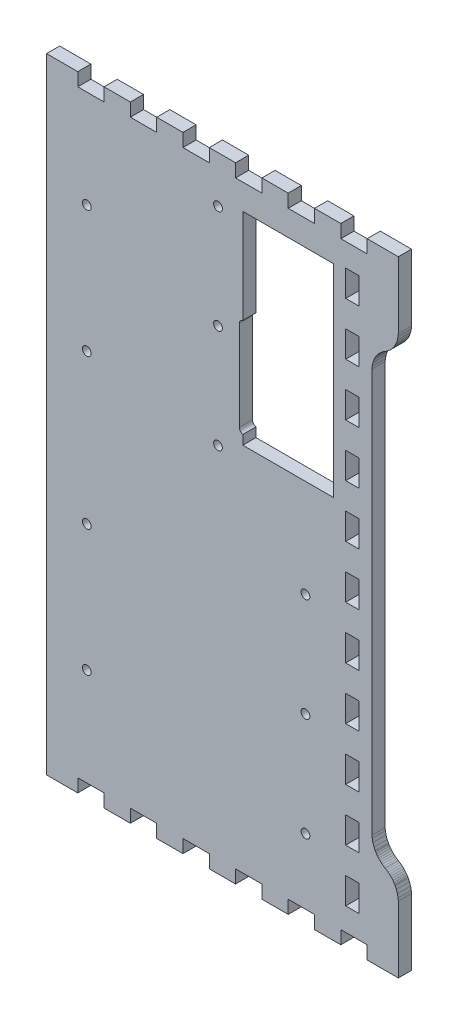
SolidWorks part; units mm, degrees
ref_plane "Front Plane" through (0, 0, 0) normal (0, 0, 1) x (1, 0, 0)
ref_plane "Top Plane" through (0, 0, 0) normal (0, 1, 0) x (1, 0, 0)
ref_plane "Right Plane" through (0, 0, 0) normal (1, 0, 0) x (0, 0, -1)
sketch "Model" plane through (0, 0, 0) normal (0, 0, 1) x (1, 0, 0)
  line L947 (1382.75, 22.8575) -> (1396.32, 22.8575)
  line L948 (1396.32, 22.8575) -> (1396.32, 28.5722)
  line L949 (1396.32, 28.5722) -> (1407.75, 28.5722)
  line L950 (1407.75, 28.5722) -> (1407.75, 22.8575)
  line L951 (1407.75, 22.8575) -> (1419.18, 22.8575)
  line L952 (1419.18, 22.8575) -> (1419.18, 28.5722)
  line L953 (1419.18, 28.5722) -> (1430.61, 28.5722)
  line L954 (1430.61, 28.5722) -> (1430.61, 22.8575)
  line L955 (1430.61, 22.8575) -> (1442.04, 22.8575)
  line L956 (1442.04, 22.8575) -> (1442.04, 28.5722)
  line L957 (1442.04, 28.5722) -> (1453.47, 28.5722)
  line L958 (1453.47, 28.5722) -> (1453.47, 22.8575)
  line L959 (1453.47, 22.8575) -> (1464.9, 22.8575)
  line L960 (1464.9, 22.8575) -> (1464.9, 28.5722)
  line L961 (1464.9, 28.5722) -> (1476.33, 28.5722)
  line L962 (1476.33, 28.5722) -> (1476.33, 22.8575)
  line L963 (1476.33, 22.8575) -> (1487.76, 22.8575)
  line L964 (1487.76, 22.8575) -> (1487.76, 28.5722)
  line L965 (1487.76, 28.5722) -> (1499.19, 28.5722)
  line L966 (1499.19, 28.5722) -> (1499.19, 22.8575)
  line L967 (1499.19, 22.8575) -> (1510.62, 22.8575)
  line L968 (1510.62, 22.8575) -> (1510.62, 28.5722)
  line L969 (1510.62, 28.5722) -> (1522.05, 28.5722)
  line L970 (1522.05, 28.5722) -> (1522.05, 22.8575)
  line L971 (1522.05, 22.8575) -> (1535.61, 22.8575)
  line L972 (1535.61, 22.8575) -> (1535.61, 28.5722)
  line L973 (1535.61, 28.5722) -> (1535.61, 51.4325)
  line L974 (1535.61, 51.4325) -> (1535.61, 51.8072)
  line L975 (1535.61, 51.8072) -> (1535.51, 52.9276)
  line L976 (1535.51, 52.9276) -> (1535.22, 54.3913)
  line L977 (1535.22, 54.3913) -> (1534.74, 55.8038)
  line L978 (1534.74, 55.8038) -> (1534.27, 56.8247)
  line L979 (1534.27, 56.8247) -> (1534.08, 57.1472)
  line L980 (1534.08, 57.1472) -> (1533.99, 57.3098)
  line L981 (1533.99, 57.3098) -> (1533.68, 57.7854)
  line L982 (1533.68, 57.7854) -> (1533.25, 58.3928)
  line L983 (1533.25, 58.3928) -> (1532.77, 58.9703)
  line L984 (1532.77, 58.9703) -> (1532.27, 59.5147)
  line L985 (1532.27, 59.5147) -> (1531.72, 60.0244)
  line L986 (1531.72, 60.0244) -> (1531.14, 60.4986)
  line L987 (1531.14, 60.4986) -> (1530.53, 60.9353)
  line L988 (1530.53, 60.9353) -> (1530.06, 61.2387)
  line L989 (1530.06, 61.2387) -> (1529.9, 61.3311)
  line L990 (1529.9, 61.3311) -> (1529.74, 61.4246)
  line L991 (1529.74, 61.4246) -> (1529.26, 61.728)
  line L992 (1529.26, 61.728) -> (1528.65, 62.1647)
  line L993 (1528.65, 62.1647) -> (1528.07, 62.6389)
  line L994 (1528.07, 62.6389) -> (1527.53, 63.1486)
  line L995 (1527.53, 63.1486) -> (1527.02, 63.693)
  line L996 (1527.02, 63.693) -> (1526.55, 64.2705)
  line L997 (1526.55, 64.2705) -> (1526.11, 64.878)
  line L998 (1526.11, 64.878) -> (1525.81, 65.3535)
  line L999 (1525.81, 65.3535) -> (1525.71, 65.5147)
  line L1000 (1525.71, 65.5147) -> (1525.53, 65.8386)
  line L1001 (1525.53, 65.8386) -> (1525.05, 66.8595)
  line L1002 (1525.05, 66.8595) -> (1524.57, 68.272)
  line L1003 (1524.57, 68.272) -> (1524.28, 69.7357)
  line L1004 (1524.28, 69.7357) -> (1524.18, 70.8561)
  line L1005 (1524.18, 70.8561) -> (1524.18, 71.2294)
  line L1006 (1524.18, 71.2294) -> (1524.18, 245.915)
  line L1007 (1524.18, 245.915) -> (1524.18, 246.29)
  line L1008 (1524.18, 246.29) -> (1524.28, 247.41)
  line L1009 (1524.28, 247.41) -> (1524.57, 248.874)
  line L1010 (1524.57, 248.874) -> (1525.05, 250.286)
  line L1011 (1525.05, 250.286) -> (1525.53, 251.307)
  line L1012 (1525.53, 251.307) -> (1525.71, 251.63)
  line L1013 (1525.71, 251.63) -> (1525.81, 251.792)
  line L1014 (1525.81, 251.792) -> (1526.11, 252.268)
  line L1015 (1526.11, 252.268) -> (1526.55, 252.876)
  line L1016 (1526.55, 252.876) -> (1527.02, 253.453)
  line L1017 (1527.02, 253.453) -> (1527.53, 253.997)
  line L1018 (1527.53, 253.997) -> (1528.07, 254.507)
  line L1019 (1528.07, 254.507) -> (1528.65, 254.981)
  line L1020 (1528.65, 254.981) -> (1529.26, 255.418)
  line L1021 (1529.26, 255.418) -> (1529.74, 255.72)
  line L1022 (1529.74, 255.72) -> (1529.9, 255.814)
  line L1023 (1529.9, 255.814) -> (1530.06, 255.907)
  line L1024 (1530.06, 255.907) -> (1530.53, 256.211)
  line L1025 (1530.53, 256.211) -> (1531.14, 256.647)
  line L1026 (1531.14, 256.647) -> (1531.72, 257.121)
  line L1027 (1531.72, 257.121) -> (1532.27, 257.631)
  line L1028 (1532.27, 257.631) -> (1532.77, 258.175)
  line L1029 (1532.77, 258.175) -> (1533.25, 258.753)
  line L1030 (1533.25, 258.753) -> (1533.68, 259.36)
  line L1031 (1533.68, 259.36) -> (1533.99, 259.836)
  line L1032 (1533.99, 259.836) -> (1534.08, 259.997)
  line L1033 (1534.08, 259.997) -> (1534.27, 260.321)
  line L1034 (1534.27, 260.321) -> (1534.74, 261.342)
  line L1035 (1534.74, 261.342) -> (1535.22, 262.755)
  line L1036 (1535.22, 262.755) -> (1535.51, 264.218)
  line L1037 (1535.51, 264.218) -> (1535.61, 265.339)
  line L1038 (1535.61, 265.339) -> (1535.61, 265.712)
  line L1039 (1535.61, 265.712) -> (1535.61, 288.572)
  line L1040 (1535.61, 288.572) -> (1535.61, 294.287)
  line L1041 (1535.61, 294.287) -> (1522.05, 294.287)
  line L1042 (1522.05, 294.287) -> (1522.05, 288.572)
  line L1043 (1522.05, 288.572) -> (1510.62, 288.572)
  line L1044 (1510.62, 288.572) -> (1510.62, 294.287)
  line L1045 (1510.62, 294.287) -> (1499.19, 294.287)
  line L1046 (1499.19, 294.287) -> (1499.19, 288.572)
  line L1047 (1499.19, 288.572) -> (1487.76, 288.572)
  line L1048 (1487.76, 288.572) -> (1487.76, 294.287)
  line L1049 (1487.76, 294.287) -> (1476.33, 294.287)
  line L1050 (1476.33, 294.287) -> (1476.33, 288.572)
  line L1051 (1476.33, 288.572) -> (1464.9, 288.572)
  line L1052 (1464.9, 288.572) -> (1464.9, 294.287)
  line L1053 (1464.9, 294.287) -> (1453.47, 294.287)
  line L1054 (1453.47, 294.287) -> (1453.47, 288.572)
  line L1055 (1453.47, 288.572) -> (1442.04, 288.572)
  line L1056 (1442.04, 288.572) -> (1442.04, 294.287)
  line L1057 (1442.04, 294.287) -> (1430.61, 294.287)
  line L1058 (1430.61, 294.287) -> (1430.61, 288.572)
  line L1059 (1430.61, 288.572) -> (1419.18, 288.572)
  line L1060 (1419.18, 288.572) -> (1419.18, 294.287)
  line L1061 (1419.18, 294.287) -> (1407.75, 294.287)
  line L1062 (1407.75, 294.287) -> (1407.75, 288.572)
  line L1063 (1407.75, 288.572) -> (1396.32, 288.572)
  line L1064 (1396.32, 288.572) -> (1396.32, 294.287)
  line L1065 (1396.32, 294.287) -> (1382.75, 294.287)
  line L1066 (1382.75, 294.287) -> (1382.75, 288.572)
  line L1067 (1382.75, 288.572) -> (1382.75, 28.5722)
  line L1068 (1382.75, 28.5722) -> (1382.75, 22.8575)
  line L1069 (1518.47, 44.2722) -> (1518.47, 38.5576)
  line L1070 (1518.47, 38.5576) -> (1512.75, 38.5576)
  line L1071 (1512.75, 38.5576) -> (1512.75, 49.9868)
  line L1072 (1512.75, 49.9868) -> (1518.47, 49.9868)
  line L1073 (1518.47, 49.9868) -> (1518.47, 44.2722)
  line L1074 (1518.47, 67.1326) -> (1518.47, 61.4179)
  line L1075 (1518.47, 61.4179) -> (1512.75, 61.4179)
  line L1076 (1512.75, 61.4179) -> (1512.75, 72.8472)
  line L1077 (1512.75, 72.8472) -> (1518.47, 72.8472)
  line L1078 (1518.47, 72.8472) -> (1518.47, 67.1326)
  line L1079 (1518.47, 89.9929) -> (1518.47, 84.2779)
  line L1080 (1518.47, 84.2779) -> (1512.75, 84.2779)
  line L1081 (1512.75, 84.2779) -> (1512.75, 95.7076)
  line L1082 (1512.75, 95.7076) -> (1518.47, 95.7076)
  line L1083 (1518.47, 95.7076) -> (1518.47, 89.9929)
  line L1084 (1518.47, 112.853) -> (1518.47, 107.137)
  line L1085 (1518.47, 107.137) -> (1512.75, 107.137)
  line L1086 (1512.75, 107.137) -> (1512.75, 118.568)
  line L1087 (1512.75, 118.568) -> (1518.47, 118.568)
  line L1088 (1518.47, 118.568) -> (1518.47, 112.853)
  line L1089 (1518.47, 135.712) -> (1518.47, 129.997)
  line L1090 (1518.47, 129.997) -> (1512.75, 129.997)
  line L1091 (1512.75, 129.997) -> (1512.75, 141.428)
  line L1092 (1512.75, 141.428) -> (1518.47, 141.428)
  line L1093 (1518.47, 141.428) -> (1518.47, 135.712)
  line L1094 (1518.47, 158.572) -> (1518.47, 152.858)
  line L1095 (1518.47, 152.858) -> (1512.75, 152.858)
  line L1096 (1512.75, 152.858) -> (1512.75, 164.287)
  line L1097 (1512.75, 164.287) -> (1518.47, 164.287)
  line L1098 (1518.47, 164.287) -> (1518.47, 158.572)
  line L1099 (1518.47, 181.433) -> (1518.47, 175.718)
  line L1100 (1518.47, 175.718) -> (1512.75, 175.718)
  line L1101 (1512.75, 175.718) -> (1512.75, 187.147)
  line L1102 (1512.75, 187.147) -> (1518.47, 187.147)
  line L1103 (1518.47, 187.147) -> (1518.47, 181.433)
  line L1104 (1518.47, 204.293) -> (1518.47, 198.578)
  line L1105 (1518.47, 198.578) -> (1512.75, 198.578)
  line L1106 (1512.75, 198.578) -> (1512.75, 210.008)
  line L1107 (1512.75, 210.008) -> (1518.47, 210.008)
  line L1108 (1518.47, 210.008) -> (1518.47, 204.293)
  line L1109 (1518.47, 227.153) -> (1518.47, 221.437)
  line L1110 (1518.47, 221.437) -> (1512.75, 221.437)
  line L1111 (1512.75, 221.437) -> (1512.75, 232.868)
  line L1112 (1512.75, 232.868) -> (1518.47, 232.868)
  line L1113 (1518.47, 232.868) -> (1518.47, 227.153)
  line L1114 (1518.47, 250.012) -> (1518.47, 244.297)
  line L1115 (1518.47, 244.297) -> (1512.75, 244.297)
  line L1116 (1512.75, 244.297) -> (1512.75, 255.728)
  line L1117 (1512.75, 255.728) -> (1518.47, 255.728)
  line L1118 (1518.47, 255.728) -> (1518.47, 250.012)
  line L1119 (1518.47, 272.872) -> (1518.47, 267.158)
  line L1120 (1518.47, 267.158) -> (1512.75, 267.158)
  line L1121 (1512.75, 267.158) -> (1512.75, 278.587)
  line L1122 (1512.75, 278.587) -> (1518.47, 278.587)
  line L1123 (1518.47, 278.587) -> (1518.47, 272.872)
extrude "Boss-Extrude1" add sketch "Model" along normal blind 5.715
sketch "Sketch1" plane through (0, 0, 0) normal (0, 0, -1) x (-1, 0, 0)
  line L24 (-1468.0398, 277.5723) -> (-1507.5398, 277.5723)
  line L25 (-1507.5398, 277.5723) -> (-1507.5398, 189.5723)
  line L26 (-1507.5398, 189.5723) -> (-1468.0398, 189.5723)
  line L27 (-1466.5398, 195.5223) -> (-1466.5398, 234.6223)
  line L29 (-1468.0398, 236.5197) -> (-1468.0398, 277.5723)
  line L40 (-1468.0398, 277.5723) -> (-1507.5398, 277.5723)
  line L41 (-1507.5398, 277.5723) -> (-1507.5398, 189.5723)
  line L42 (-1507.5398, 189.5723) -> (-1468.0398, 189.5723)
  line L43 (-1466.5398, 195.5223) -> (-1466.5398, 234.6223)
  line L45 (-1468.0398, 236.5197) -> (-1468.0398, 277.5723)
  line L55 (-1468.0398, 189.5723) -> (-1468.0398, 193.6249)
  line L56 (-1468.0398, 189.5723) -> (-1468.0398, 193.6249)
  arc A2 (-1468.0398, 193.6249) -> (-1466.5398, 195.5223) centre (-1468.4898, 195.5223) ccw
  arc A4 (-1466.5398, 234.6223) -> (-1468.0398, 236.5197) centre (-1468.4898, 234.6223) ccw
  arc A5 (-1466.5398, 234.6223) -> (-1468.0398, 236.5197) centre (-1468.4898, 234.6223) ccw
  arc A10 (-1468.0398, 193.6249) -> (-1466.5398, 195.5223) centre (-1468.4898, 195.5223) ccw
  dimension "D1" = 0.5
extrude "Cut-Extrude1" cut sketch "Sketch1" against normal through all
sketch "Sketch2" plane through (0, 0, 5.715) normal (0, 0, 1) x (1, 0, 0)
  point P0 (1400.25, 71.0721)
  point P1 (1400.25, 126.0721)
  point P3 (1400.25, 191.0721)
  point P5 (1400.25, 246.0721)
  point P7 (1457.2548, 184.072)
  point P9 (1457.2548, 229.072)
  point P11 (1457.2548, 274.072)
  point P13 (1495.2548, 57.0223)
  point P15 (1495.2548, 102.0223)
  point P17 (1495.2548, 147.0223)
hole_wizard "#6 Clearance Hole1" positions "Sketch5" profile "Sketch6" hole size "#6" standard "ANSI Inch" end condition through all
sketch "Sketch5" plane through (0, 0, 0) normal (0, 0, -1) x (-1, 0, 0)
  point P0 (-1400.25, 246.0721)
  point P3 (-1400.25, 191.0721)
  point P6 (-1400.25, 126.0721)
  point P9 (-1400.25, 71.0721)
  point P12 (-1457.2548, 274.072)
  point P15 (-1457.2548, 229.072)
  point P18 (-1457.2548, 184.072)
  point P21 (-1495.2548, 147.0223)
  point P24 (-1495.2548, 102.0223)
  point P27 (-1495.2548, 57.0223)
sketch "Sketch6" plane through (1400.25, 246.0721, 0) normal (1, 0, 0) x (0, 1, 0)
  line L0 (0, 0) -> (0, 5.715)
  line L1 (0, 5.715) -> (1.8986, 5.715)
  line L2 (1.8986, 5.715) -> (1.8986, 0)
  line L5 (1.8986, 0) -> (0, 0)
  line L11 (0, -6.35) -> (0, 107.95) construction
  dimension "Thru Hole Dia." = 3.7973
  dimension "Thru Hole Depth" = 5.715
